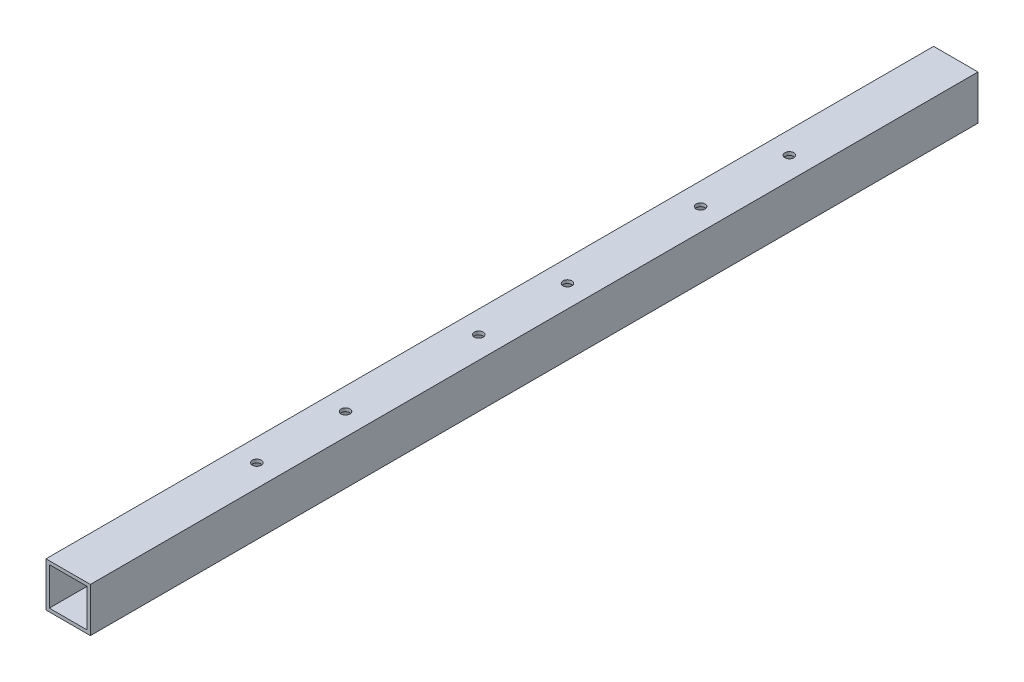
SolidWorks part; units mm, degrees
material "Stainless Steel (ferritic)"
ref_plane "Front Plane" through (0, 0, 0) normal (0, 0, 1) x (1, 0, 0)
ref_plane "Top Plane" through (0, 0, 0) normal (0, 1, 0) x (1, 0, 0)
ref_plane "Right Plane" through (0, 0, 0) normal (1, 0, 0) x (0, 0, -1)
sketch "Sketch1" plane through (0, 0, 0) normal (0, 0, 1) x (1, 0, 0)
  line L1 (-10, 10) -> (10, 10)
  line L2 (-10, 10) -> (-10, -10)
  line L3 (-10, -10) -> (10, -10)
  line L4 (10, 10) -> (10, -10)
  line L5 (-10, 10) -> (10, -10) construction
  line L6 (-10, -10) -> (10, 10) construction
  point P0 (0, 0)
extrude "Boss-Extrude1" add sketch "Sketch1" along normal blind 400
sketch "Sketch2" plane through (0, 0, 0) normal (0, 0, -1) x (-1, 0, 0)
  line L1 (-8.5, 8.5) -> (8.5, 8.5)
  line L2 (-8.5, 8.5) -> (-8.5, -8.5)
  line L3 (-8.5, -8.5) -> (8.5, -8.5)
  line L4 (8.5, 8.5) -> (8.5, -8.5)
  line L5 (-8.5, 8.5) -> (8.5, -8.5) construction
  line L6 (-8.5, -8.5) -> (8.5, 8.5) construction
  point P0 (0, 0)
extrude "Cut-Extrude1" cut sketch "Sketch2" against normal blind 400
sketch "Sketch3" plane through (0, 10, 0) normal (0, 1, 0) x (1, 0, 0)
  circle A0 centre (0, -75) radius 2
extrude "Cut-Extrude2" cut sketch "Sketch3" against normal blind 25
sketch "Sketch4" plane through (0, 10, 0) normal (0, 1, 0) x (1, 0, 0)
  circle A0 centre (0, -115) radius 2
extrude "Cut-Extrude3" cut sketch "Sketch4" against normal blind 25
pattern_linear "LPattern1" count 3 spacing 100 along (0, 0, 1) of "Cut-Extrude3", "Cut-Extrude2"
